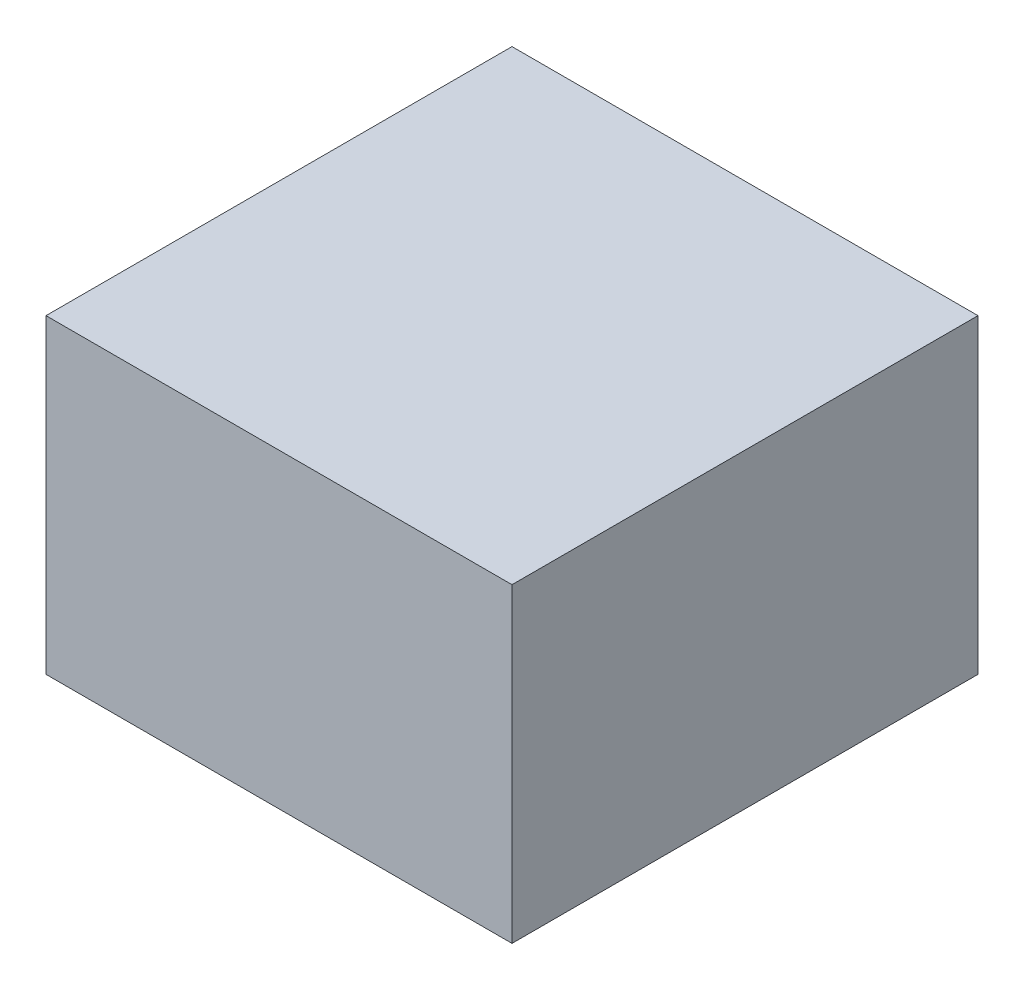
SolidWorks part; units mm, degrees
ref_plane "Front Plane" through (0, 0, 0) normal (0, 0, 1) x (1, 0, 0)
ref_plane "Top Plane" through (0, 0, 0) normal (0, 1, 0) x (1, 0, 0)
ref_plane "Right Plane" through (0, 0, 0) normal (1, 0, 0) x (0, 0, -1)
sketch "Sketch1" plane through (0, 0, 0) normal (0, 1, 0) x (1, 0, 0)
  line L1 (0, 0) -> (76.2, 0)
  line L2 (0, 0) -> (0, -76.2)
  line L3 (0, -76.2) -> (76.2, -76.2)
  line L4 (76.2, 0) -> (76.2, -76.2)
  dimension "D1" = 76.2
extrude "Boss-Extrude1" add sketch "Sketch1" along normal blind 50.8
